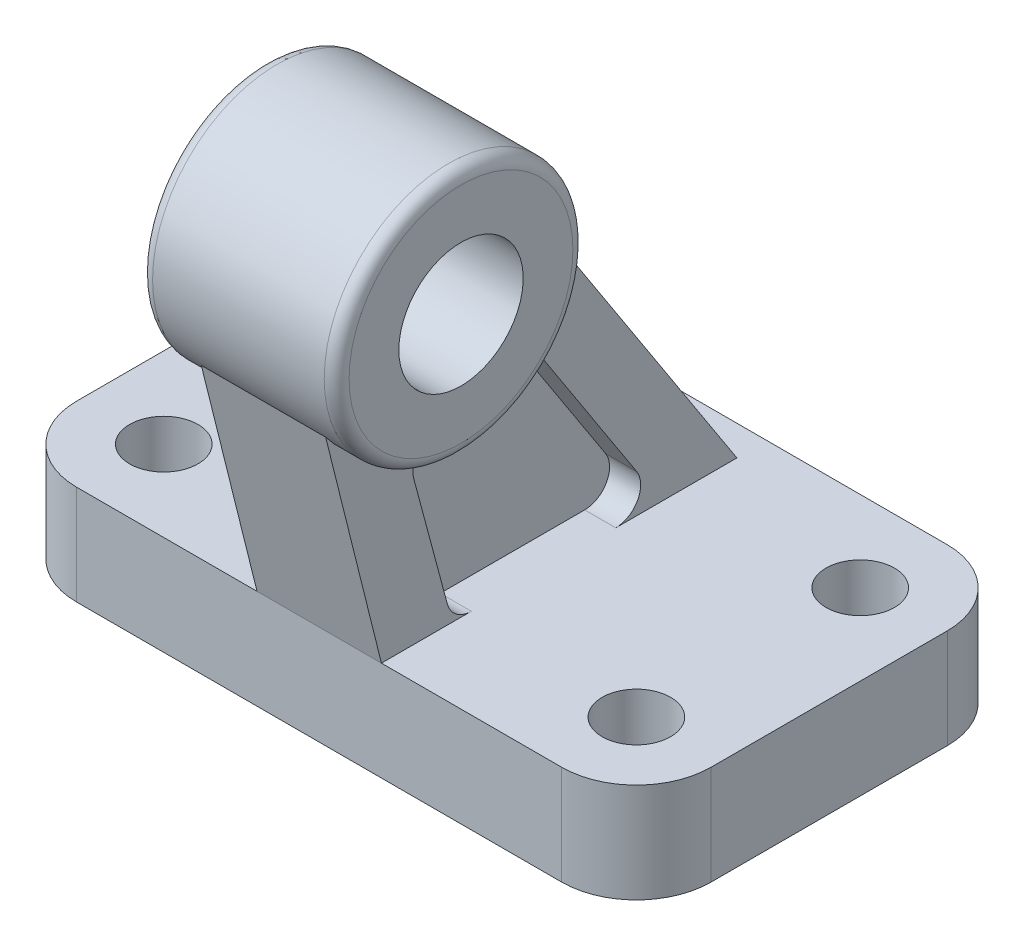
SolidWorks part; units mm, degrees
ref_plane "Front Plane" through (0, 0, 0) normal (0, 0, 1) x (1, 0, 0)
ref_plane "Top Plane" through (0, 0, 0) normal (0, 1, 0) x (1, 0, 0)
ref_plane "Right Plane" through (0, 0, 0) normal (1, 0, 0) x (0, 0, -1)
ref_plane "Plane1" through (0, 0, 0) normal (0, 1, 0) x (1, 0, 0)
sketch "Sketch1" plane through (0, 0, 0) normal (0, 1, 0) x (1, 0, 0)
  line L0 (-19.5, -15.5) -> (19.5, -15.5)
  line L1 (25.5, -9.5) -> (25.5, 9.5)
  line L2 (19.5, 15.5) -> (-19.5, 15.5)
  line L3 (-25.5, 9.5) -> (-25.5, -9.5)
  arc A0 (-25.5, -9.5) -> (-19.5, -15.5) centre (-19.5, -9.5) ccw
  arc A1 (19.5, -15.5) -> (25.5, -9.5) centre (19.5, -9.5) ccw
  arc A2 (25.5, 9.5) -> (19.5, 15.5) centre (19.5, 9.5) ccw
  arc A3 (-19.5, 15.5) -> (-25.5, 9.5) centre (-19.5, 9.5) ccw
  circle A4 centre (19, 9) radius 2.75
  circle A5 centre (19, -9) radius 2.75
  circle A6 centre (-19, 9) radius 2.75
  circle A7 centre (-19, -9) radius 2.75
extrude "Boss-Extrude1" add sketch "Sketch1" along normal blind 8
ref_plane "Plane2" through (0, 0, 0) normal (1, 0, 0) x (0, 0, -1)
sketch "Sketch2" plane through (0, 0, 0) normal (1, 0, 0) x (0, 0, -1)
  line L0 (-20.3578, 27.4838) -> (-15.5, 8)
  line L1 (-15.5, 8) -> (13.0858, 8)
  line L2 (13.0858, 8) -> (-2.5, 32)
  arc A0 (-2.5, 32) -> (-20.3578, 27.4838) centre (-12, 32) cw
extrude "Boss-Extrude2" add sketch "Sketch2" against normal blind 5 and the other way blind 5
ref_plane "Plane3" through (5, 0, 0) normal (1, 0, 0) x (0, 0, -1)
sketch "Sketch3" plane through (5, 0, 0) normal (1, 0, 0) x (0, 0, -1)
  line L0 (-12.8947, 19.5273) -> (-10.2032, 9.4824)
  line L1 (-8.2713, 8) -> (3.3442, 8)
  line L2 (5.0216, 11.0893) -> (-3.0612, 23.5357)
  arc A0 (-11.1357, 22.0374) -> (-12.8947, 19.5273) centre (-10.9629, 20.0449) ccw
  arc A1 (-10.2032, 9.4824) -> (-8.2713, 8) centre (-8.2713, 10) ccw
  arc A2 (3.3442, 8) -> (5.0216, 11.0893) centre (3.3442, 10) ccw
  arc A3 (-3.0612, 23.5357) -> (-5.9488, 24.0387) centre (-4.7385, 22.4464) ccw
  arc A4 (-5.9488, 24.0387) -> (-11.1357, 22.0374) centre (-12, 32) cw
extrude "Cut-Extrude1" cut sketch "Sketch3" against normal blind 2.5
ref_plane "Plane4" through (-5, 0, 0) normal (1, 0, 0) x (0, 0, -1)
sketch "Sketch4" plane through (-5, 0, 0) normal (1, 0, 0) x (0, 0, -1)
  line L0 (-12.8947, 19.5273) -> (-10.2032, 9.4824)
  line L1 (-8.2713, 8) -> (3.3442, 8)
  line L2 (5.0216, 11.0893) -> (-3.0612, 23.5357)
  arc A0 (-11.1357, 22.0374) -> (-12.8947, 19.5273) centre (-10.9629, 20.0449) ccw
  arc A1 (-10.2032, 9.4824) -> (-8.2713, 8) centre (-8.2713, 10) ccw
  arc A2 (3.3442, 8) -> (5.0216, 11.0893) centre (3.3442, 10) ccw
  arc A3 (-3.0612, 23.5357) -> (-5.9488, 24.0387) centre (-4.7385, 22.4464) ccw
  arc A4 (-5.9488, 24.0387) -> (-11.1357, 22.0374) centre (-12, 32) cw
extrude "Cut-Extrude2" cut sketch "Sketch4" along normal blind 2.5
ref_plane "Plane5" through (0, 0, 12) normal (0, 0, 1) x (1, 0, 0)
sketch "Sketch5" plane through (0, 0, 12) normal (0, 0, 1) x (1, 0, 0)
  line L0 (-7.9, 41) -> (-7.9, 37)
  line L1 (-7.9, 37) -> (7.9, 37)
  line L2 (7.9, 37) -> (7.9, 41)
  line L3 (6.9, 42) -> (-6.9, 42)
  line L4 (7.9, 32) -> (-7.9, 32) construction
  arc A0 (7.9, 41) -> (6.9, 42) centre (6.9, 41) ccw
  arc A1 (-6.9, 42) -> (-7.9, 41) centre (-6.9, 41) ccw
revolve "Revolve1" add sketch "Sketch5" angle 360 about L4
ref_plane "Plane6" through (0, 0, 0) normal (0, 1, 0) x (1, 0, 0)
sketch "Sketch6" plane through (0, 0, 0) normal (0, 1, 0) x (1, 0, 0)
  line L0 (-20.5, 0.0139) -> (-20.5, -0.0139)
  line L1 (-10.0557, -10) -> (10.0557, -10)
  line L2 (20.5, -0.0139) -> (20.5, 0.0139)
  line L3 (10.0557, 10) -> (-10.0557, 10)
  arc A0 (-20.5, -0.0139) -> (-18.6111, -2.0108) centre (-18.5, -0.0139) ccw
  arc A1 (-18.6111, -2.0108) -> (-12.0433, -8.2222) centre (-19, -9) cw
  arc A2 (-12.0433, -8.2222) -> (-10.0557, -10) centre (-10.0557, -8) ccw
  arc A3 (10.0557, -10) -> (12.0433, -8.2222) centre (10.0557, -8) ccw
  arc A4 (12.0433, -8.2222) -> (18.6111, -2.0108) centre (19, -9) cw
  arc A5 (18.6111, -2.0108) -> (20.5, -0.0139) centre (18.5, -0.0139) ccw
  arc A6 (20.5, 0.0139) -> (18.6111, 2.0108) centre (18.5, 0.0139) ccw
  arc A7 (18.6111, 2.0108) -> (12.0433, 8.2222) centre (19, 9) cw
  arc A8 (12.0433, 8.2222) -> (10.0557, 10) centre (10.0557, 8) ccw
  arc A9 (-10.0557, 10) -> (-12.0433, 8.2222) centre (-10.0557, 8) ccw
  arc A10 (-12.0433, 8.2222) -> (-18.6111, 2.0108) centre (-19, 9) cw
  arc A11 (-18.6111, 2.0108) -> (-20.5, 0.0139) centre (-18.5, 0.0139) ccw
extrude "Cut-Extrude3" cut sketch "Sketch6" along normal blind 3.5
